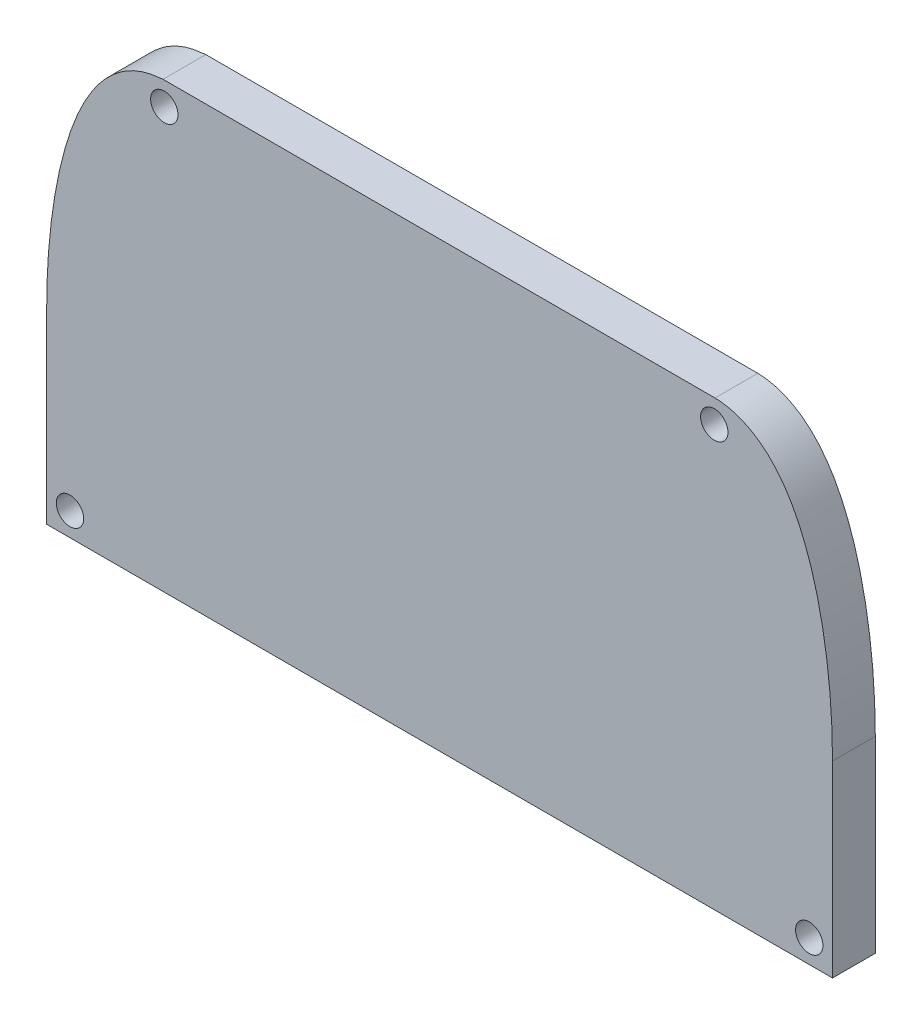
SolidWorks part; units mm, degrees
ref_plane "Front Plane" through (0, 0, 0) normal (0, 0, 1) x (1, 0, 0)
ref_plane "Top Plane" through (0, 0, 0) normal (0, 1, 0) x (1, 0, 0)
ref_plane "Right Plane" through (0, 0, 0) normal (1, 0, 0) x (0, 0, -1)
sketch "Sketch1" plane through (0, 0, 0) normal (0, 0, 1) x (1, 0, 0)
  line L0 (-29, 6.1775) -> (-29, 20.2039) construction
  line L1 (-29, 6.1775) -> (29, 6.1775) construction
  line L2 (29, 20.2039) -> (29, 6.1775) construction
  line L3 (-20.2196, 39.1775) -> (20.1267, 39.1775) construction
  line L4 (-29, 6.1775) -> (-29, 20.2039) construction
  line L5 (-29, 6.1775) -> (29, 6.1775) construction
  line L6 (29, 20.2039) -> (29, 6.1775) construction
  line L7 (-20.2196, 39.1775) -> (20.1267, 39.1775) construction
  line L8 (-20.2031, 38.8775) -> (20.1172, 38.8775)
  line L9 (28.7, 20.2019) -> (28.7, 6.4775)
  line L10 (-28.7, 6.4775) -> (28.7, 6.4775)
  line L11 (-28.7, 6.4775) -> (-28.7, 20.202)
  spline S0 degree 2 poles (-30.7786, -979.7937) (-29.523, 0.3219) (-28.9753, 21.6255) (-28.956, 22.3771) (-28.9167, 23.0453) (-28.8758, 23.7425) (-28.8098, 24.4628) (-28.7437, 25.1849) (-28.6586, 25.8762) (-28.48, 27.3286) (-28.2121, 28.6679) (-27.9174, 30.1416) (-27.5367, 31.4021) (-27.0956, 32.8627) (-26.54, 34.0556) (-26.2171, 34.7489) (-25.8726, 35.325) (-25.4881, 35.968) (-25.0615, 36.5044) (-24.6042, 37.0792) (-24.0818, 37.5451) (-23.8077, 37.7895) (-23.5307, 37.9927) (-23.2417, 38.2049) (-22.9324, 38.3835) (-22.6103, 38.5695) (-22.2891, 38.7054) (-21.9641, 38.843) (-21.6205, 38.94) (-21.3002, 39.0305) (-20.9286, 39.0899) (-20.7579, 39.1171) (-20.5753, 39.1381) (-18.3011, 39.3998) (973.7748, 148.004) knots -2.748169 -2.748169 -2.748169 0.0625 0.0625 0.125 0.125 0.1875 0.1875 0.25 0.25 0.375 0.375 0.5 0.5 0.625 0.625 0.6875 0.6875 0.75 0.75 0.8125 0.8125 0.84375 0.84375 0.875 0.875 0.90625 0.90625 0.9375 0.9375 0.96875 0.96875 0.984375 0.984375 1.914543 1.914543 1.914543 only from (-29, 20.2039) to (-20.2196, 39.1775) construction
  spline S1 degree 2 poles (-978.5189, 91.0927) (12.7252, 39.7941) (20.4852, 39.1529) (20.6703, 39.1376) (20.8404, 39.113) (21.2069, 39.06) (21.537, 38.9685) (21.7643, 38.9054) (21.9906, 38.8219) (22.4388, 38.6565) (22.8602, 38.4209) (23.1749, 38.245) (23.4635, 38.0404) (23.748, 37.8387) (24.0261, 37.596) (24.5413, 37.1466) (25.0135, 36.5637) (25.3594, 36.1367) (25.6787, 35.638) (25.9078, 35.2802) (26.1167, 34.8974) (26.3118, 34.5397) (26.5032, 34.134) (27.0665, 32.9404) (27.5124, 31.4821) (27.9021, 30.2074) (28.2027, 28.7148) (28.4749, 27.3631) (28.6558, 25.8992) (28.7415, 25.206) (28.8083, 24.4794) (28.8748, 23.7559) (28.9161, 23.0565) (28.9558, 22.3839) (28.9752, 21.6311) (29.5264, 0.2624) (30.6368, -979.7884) knots -1.208096 -1.208096 -1.208096 0.015625 0.015625 0.03125 0.03125 0.0625 0.0625 0.083333 0.083333 0.125 0.125 0.15625 0.15625 0.1875 0.1875 0.25 0.25 0.3 0.3 0.3375 0.3375 0.375 0.375 0.5 0.5 0.625 0.625 0.75 0.75 0.8125 0.8125 0.875 0.875 0.9375 0.9375 3.743951 3.743951 3.743951 only from (20.1267, 39.1775) to (29, 20.2039) construction
  spline S2 degree 2 poles (-29, 20.2039) (-28.9875, 21.1518) (-28.9753, 21.6255) (-28.956, 22.3771) (-28.9167, 23.0453) (-28.8758, 23.7425) (-28.8098, 24.4628) (-28.7437, 25.1849) (-28.6586, 25.8762) (-28.48, 27.3286) (-28.2121, 28.6679) (-27.9174, 30.1416) (-27.5367, 31.4021) (-27.0956, 32.8627) (-26.54, 34.0556) (-26.2171, 34.7489) (-25.8726, 35.325) (-25.4881, 35.968) (-25.0615, 36.5044) (-24.6042, 37.0792) (-24.0818, 37.5451) (-23.8077, 37.7895) (-23.5307, 37.9927) (-23.2417, 38.2049) (-22.9324, 38.3835) (-22.6103, 38.5695) (-22.2891, 38.7054) (-21.9641, 38.843) (-21.6205, 38.94) (-21.3002, 39.0305) (-20.9286, 39.0899) (-20.7579, 39.1171) (-20.5753, 39.1381) (-20.5371, 39.1425) (-20.2196, 39.1775) knots 0 0 0 0.0625 0.0625 0.125 0.125 0.1875 0.1875 0.25 0.25 0.375 0.375 0.5 0.5 0.625 0.625 0.6875 0.6875 0.75 0.75 0.8125 0.8125 0.84375 0.84375 0.875 0.875 0.90625 0.90625 0.9375 0.9375 0.96875 0.96875 0.984375 0.984375 1 1 1 construction
  spline S3 degree 2 poles (20.1267, 39.1775) (20.3861, 39.1611) (20.4852, 39.1529) (20.6703, 39.1376) (20.8404, 39.113) (21.2069, 39.06) (21.537, 38.9685) (21.7643, 38.9054) (21.9906, 38.8219) (22.4388, 38.6565) (22.8602, 38.4209) (23.1749, 38.245) (23.4635, 38.0404) (23.748, 37.8387) (24.0261, 37.596) (24.5413, 37.1466) (25.0135, 36.5637) (25.3594, 36.1367) (25.6787, 35.638) (25.9078, 35.2802) (26.1167, 34.8974) (26.3118, 34.5397) (26.5032, 34.134) (27.0665, 32.9404) (27.5124, 31.4821) (27.9021, 30.2074) (28.2027, 28.7148) (28.4749, 27.3631) (28.6558, 25.8992) (28.7415, 25.206) (28.8083, 24.4794) (28.8748, 23.7559) (28.9161, 23.0565) (28.9558, 22.3839) (28.9752, 21.6311) (28.9874, 21.1552) (29, 20.2039) knots 0 0 0 0.015625 0.015625 0.03125 0.03125 0.0625 0.0625 0.083333 0.083333 0.125 0.125 0.15625 0.15625 0.1875 0.1875 0.25 0.25 0.3 0.3 0.3375 0.3375 0.375 0.375 0.5 0.5 0.625 0.625 0.75 0.75 0.8125 0.8125 0.875 0.875 0.9375 0.9375 1 1 1 construction
  spline S4 degree 1 poles (-28.7, 20.202) (-20.2031, 38.8775) knots 0 0 1 1 construction
  spline S5 degree 1 poles (20.1172, 38.8775) (28.7, 20.2019) knots 0 0 1 1 construction
  spline S6 degree 2 poles (-28.7, 20.202) (-28.6922, 20.7942) (-28.6822, 21.3197) (-28.6783, 21.4975) (-28.6757, 21.6076) (-28.6703, 21.8063) (-28.6632, 22.032) (-28.6482, 22.436) (-28.6106, 23.1928) (-28.5163, 24.4382) (-28.3675, 25.8348) (-28.1922, 27.0817) (-28.0466, 27.9396) (-27.9221, 28.5975) (-27.7681, 29.3289) (-27.607, 30.0158) (-27.4336, 30.6825) (-27.2573, 31.2983) (-27.0269, 32.0231) (-26.7898, 32.6894) (-26.536, 33.3294) (-26.2795, 33.9133) (-25.9472, 34.5878) (-25.627, 35.1612) (-25.2342, 35.7761) (-24.8389, 36.3128) (-24.3769, 36.8495) (-23.7716, 37.4401) (-22.8103, 38.1543) (-21.7788, 38.594) (-21.2366, 38.7293) (-20.6299, 38.8425) (-20.2031, 38.8775) knots 0.000065 0.000065 0.000065 0.039109 0.050823 0.058631 0.06644 0.074249 0.085962 0.109389 0.156242 0.218712 0.281182 0.328035 0.35927 0.390506 0.421741 0.452976 0.484211 0.515447 0.546682 0.577917 0.609152 0.640387 0.671623 0.702858 0.734093 0.765328 0.796563 0.843416 0.905887 0.944931 0.960548 0.999592 0.999592 0.999592
  spline S7 degree 2 poles (20.1172, 38.8775) (21.1567, 38.8508) (22.7359, 38.1911) (23.7199, 37.4862) (24.3174, 36.9129) (24.7922, 36.3709) (25.1938, 35.8341) (25.5802, 35.2389) (25.8807, 34.7085) (26.076, 34.3296) (26.2758, 33.9175) (26.5028, 33.408) (26.76, 32.768) (27.0001, 32.1022) (27.2326, 31.38) (27.4136, 30.7553) (27.5908, 30.081) (27.7554, 29.3857) (27.9128, 28.6444) (28.0391, 27.981) (28.187, 27.1155) (28.3648, 25.8575) (28.5147, 24.4551) (28.6098, 23.2054) (28.6478, 22.4441) (28.663, 22.0387) (28.6701, 21.8124) (28.6756, 21.6134) (28.6782, 21.5026) (28.6822, 21.3241) (28.6921, 20.7964) (28.7, 20.2019) knots 0.000288 0.000288 0.000288 0.094005 0.156483 0.203341 0.23458 0.265819 0.297058 0.328297 0.351726 0.367346 0.390775 0.422014 0.453253 0.484492 0.515731 0.54697 0.578209 0.609448 0.640687 0.671926 0.718784 0.781262 0.84374 0.890599 0.914028 0.925742 0.933552 0.941362 0.949172 0.960886 0.999935 0.999935 0.999935
  dimension "D1" = 0.3
extrude "Boss-Extrude1" add sketch "Sketch1" along normal blind 3.125
sketch "Sketch2" plane through (0, 0, 3.125) normal (0, 0, 1) x (1, 0, 0)
  line L4 (-28.7, 20.202) -> (-28.7, 6.4775)
  line L5 (-28.7, 6.4775) -> (28.7, 6.4775)
  line L6 (28.7, 6.4775) -> (28.7, 20.2019)
  line L7 (20.1172, 38.8775) -> (-20.2031, 38.8775)
  line L8 (-28.7, 20.202) -> (-28.7, 6.4775)
  line L9 (-28.7, 6.4775) -> (28.7, 6.4775)
  line L10 (28.7, 6.4775) -> (28.7, 20.2019)
  line L11 (20.1172, 38.8775) -> (-20.2031, 38.8775)
  circle A0 centre (-27, 8.1775) radius 0.8 construction
  circle A1 centre (27, 8.1775) radius 0.8 construction
  circle A2 centre (20.0628, 37.1775) radius 0.8 construction
  circle A3 centre (-20.1097, 37.1775) radius 0.8 construction
  circle A4 centre (-27, 8.1775) radius 0.8 construction
  circle A5 centre (27, 8.1775) radius 0.8 construction
  circle A6 centre (20.0628, 37.1775) radius 0.8 construction
  circle A7 centre (-20.1097, 37.1775) radius 0.8 construction
  circle A8 centre (-27, 8.1775) radius 1
  circle A9 centre (-20.1097, 37.1775) radius 1
  circle A10 centre (20.0628, 37.1775) radius 1
  circle A11 centre (27, 8.1775) radius 1
  spline S2 degree 2 poles (-126.6261, -1956.9065) (70.069, 55.7664) (-21.2366, 38.7293) (-21.7788, 38.594) (-22.8103, 38.1543) (-23.7716, 37.4401) (-24.3769, 36.8495) (-24.8389, 36.3128) (-25.2342, 35.7761) (-25.627, 35.1612) (-25.9472, 34.5878) (-26.2795, 33.9133) (-26.536, 33.3294) (-26.7898, 32.6894) (-27.0269, 32.0231) (-27.2573, 31.2983) (-27.4336, 30.6825) (-27.607, 30.0158) (-27.7681, 29.3289) (-27.9221, 28.5975) (-28.0466, 27.9396) (-28.1922, 27.0817) (-28.3675, 25.8348) (-28.5163, 24.4382) (-28.6106, 23.1928) (-28.6482, 22.436) (-28.6632, 22.032) (-28.6703, 21.8063) (-28.6757, 21.6076) (-28.6783, 21.4975) (-28.6822, 21.3197) (-29.4557, -19.6503) (-32.4179, -1979.7508) knots -8.17241 -8.17241 -8.17241 0.039109 0.054727 0.093771 0.156242 0.203094 0.23433 0.265565 0.2968 0.328035 0.35927 0.390506 0.421741 0.452976 0.484211 0.515447 0.546682 0.577917 0.609152 0.640387 0.671623 0.718475 0.780946 0.843416 0.890269 0.913696 0.925409 0.933218 0.941026 0.948835 0.960548 4.905979 4.905979 4.905979 only from (-20.2031, 38.8775) to (-28.7, 20.202)
  spline S3 degree 2 poles (32.1288, -1979.7425) (29.4589, -19.7543) (28.6822, 21.3241) (28.6782, 21.5026) (28.6756, 21.6134) (28.6701, 21.8124) (28.663, 22.0387) (28.6478, 22.4441) (28.6098, 23.2054) (28.5147, 24.4551) (28.3648, 25.8575) (28.187, 27.1155) (28.0391, 27.981) (27.9128, 28.6444) (27.7554, 29.3857) (27.5908, 30.081) (27.4136, 30.7553) (27.2326, 31.38) (27.0001, 32.1022) (26.76, 32.768) (26.5028, 33.408) (26.2758, 33.9175) (26.076, 34.3296) (25.8807, 34.7085) (25.5802, 35.2389) (25.1938, 35.8341) (24.7922, 36.3709) (24.3174, 36.9129) (23.7199, 37.4862) (22.7359, 38.1911) (-46.8806, 67.2716) (-604.1599, -1860.2407) knots -3.900441 -3.900441 -3.900441 0.039337 0.051051 0.058861 0.066671 0.074481 0.086195 0.109624 0.156483 0.218961 0.281439 0.328297 0.359536 0.390775 0.422014 0.453253 0.484492 0.515731 0.54697 0.578209 0.609448 0.632877 0.648497 0.671926 0.703165 0.734404 0.765643 0.796882 0.84374 0.906218 7.729615 7.729615 7.729615 only from (28.7, 20.2019) to (20.1172, 38.8775)
  spline S4 degree 2 poles (-20.2031, 38.8775) (-20.6299, 38.8425) (-21.2366, 38.7293) (-21.7788, 38.594) (-22.8103, 38.1543) (-23.7716, 37.4401) (-24.3769, 36.8495) (-24.8389, 36.3128) (-25.2342, 35.7761) (-25.627, 35.1612) (-25.9472, 34.5878) (-26.2795, 33.9133) (-26.536, 33.3294) (-26.7898, 32.6894) (-27.0269, 32.0231) (-27.2573, 31.2983) (-27.4336, 30.6825) (-27.607, 30.0158) (-27.7681, 29.3289) (-27.9221, 28.5975) (-28.0466, 27.9396) (-28.1922, 27.0817) (-28.3675, 25.8348) (-28.5163, 24.4382) (-28.6106, 23.1928) (-28.6482, 22.436) (-28.6632, 22.032) (-28.6703, 21.8063) (-28.6757, 21.6076) (-28.6783, 21.4975) (-28.6822, 21.3197) (-28.6922, 20.7942) (-28.7, 20.202) knots 0.000065 0.000065 0.000065 0.039109 0.054727 0.093771 0.156242 0.203094 0.23433 0.265565 0.2968 0.328035 0.35927 0.390506 0.421741 0.452976 0.484211 0.515447 0.546682 0.577917 0.609152 0.640387 0.671623 0.718475 0.780946 0.843416 0.890269 0.913696 0.925409 0.933218 0.941026 0.948835 0.960548 0.999592 0.999592 0.999592
  spline S5 degree 2 poles (28.7, 20.2019) (28.6921, 20.7964) (28.6822, 21.3241) (28.6782, 21.5026) (28.6756, 21.6134) (28.6701, 21.8124) (28.663, 22.0387) (28.6478, 22.4441) (28.6098, 23.2054) (28.5147, 24.4551) (28.3648, 25.8575) (28.187, 27.1155) (28.0391, 27.981) (27.9128, 28.6444) (27.7554, 29.3857) (27.5908, 30.081) (27.4136, 30.7553) (27.2326, 31.38) (27.0001, 32.1022) (26.76, 32.768) (26.5028, 33.408) (26.2758, 33.9175) (26.076, 34.3296) (25.8807, 34.7085) (25.5802, 35.2389) (25.1938, 35.8341) (24.7922, 36.3709) (24.3174, 36.9129) (23.7199, 37.4862) (22.7359, 38.1911) (21.1567, 38.8508) (20.1172, 38.8775) knots 0.000288 0.000288 0.000288 0.039337 0.051051 0.058861 0.066671 0.074481 0.086195 0.109624 0.156483 0.218961 0.281439 0.328297 0.359536 0.390775 0.422014 0.453253 0.484492 0.515731 0.54697 0.578209 0.609448 0.632877 0.648497 0.671926 0.703165 0.734404 0.765643 0.796882 0.84374 0.906218 0.999935 0.999935 0.999935
  dimension "D1" = 0
  dimension "D2" = 0.2
extrude "Cut-Extrude1" cut sketch "Sketch2" against normal through all contours A8 | A9 | A10 | A11
